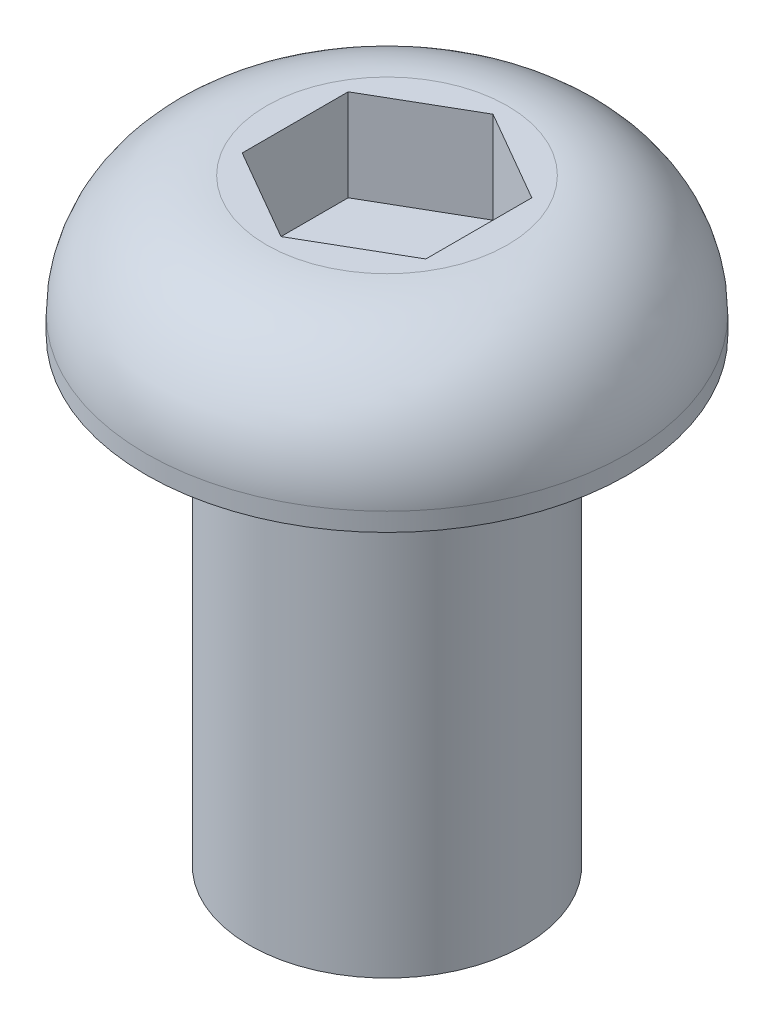
SolidWorks part; units mm, degrees
ref_plane "Plano frontal" through (0, 0, 0) normal (0, 0, 1) x (1, 0, 0)
ref_plane "Plano superior" through (0, 0, 0) normal (0, 1, 0) x (1, 0, 0)
ref_plane "Plano direito" through (0, 0, 0) normal (1, 0, 0) x (0, 0, -1)
sketch "Esboço1" plane through (0, 0, 0) normal (0, 0, 1) x (1, 0, 0)
  line L0 (0, 0) -> (6, 0)
  line L1 (6, 0) -> (6, 20)
  line L2 (6, 20) -> (10.5, 20)
  line L3 (10.5, 20) -> (10.5, 20.8)
  line L4 (5.25, 26.05) -> (0, 26.05)
  line L5 (0, 26.05) -> (0, 0) construction
  line L6 (0, 0) -> (0, 26.05)
  arc A0 (10.5, 20.8) -> (5.25, 26.05) centre (5.25, 20.8) ccw
  dimension "D1" = 21
  dimension "D2" = 12
  dimension "D3" = 0.8
  dimension "D4" = 10.5
  dimension "D5" = 20
revolve "Revolução1" add sketch "Esboço1" angle 360 about L5
sketch "Esboço2" plane through (0, 26.05, 0) normal (0, 1, 0) x (1, 0, 0)
  line L1 (-4, -2.3094) -> (0, -4.6188)
  line L2 (0, -4.6188) -> (4, -2.3094)
  line L3 (4, -2.3094) -> (4, 2.3094)
  line L4 (4, 2.3094) -> (0, 4.6188)
  line L5 (0, 4.6188) -> (-4, 2.3094)
  line L6 (-4, 2.3094) -> (-4, -2.3094)
  circle A0 centre (0, 0) radius 4 construction
  dimension "D1" = 8
extrude "Corte-extrusão1" cut sketch "Esboço2" against normal blind 4
